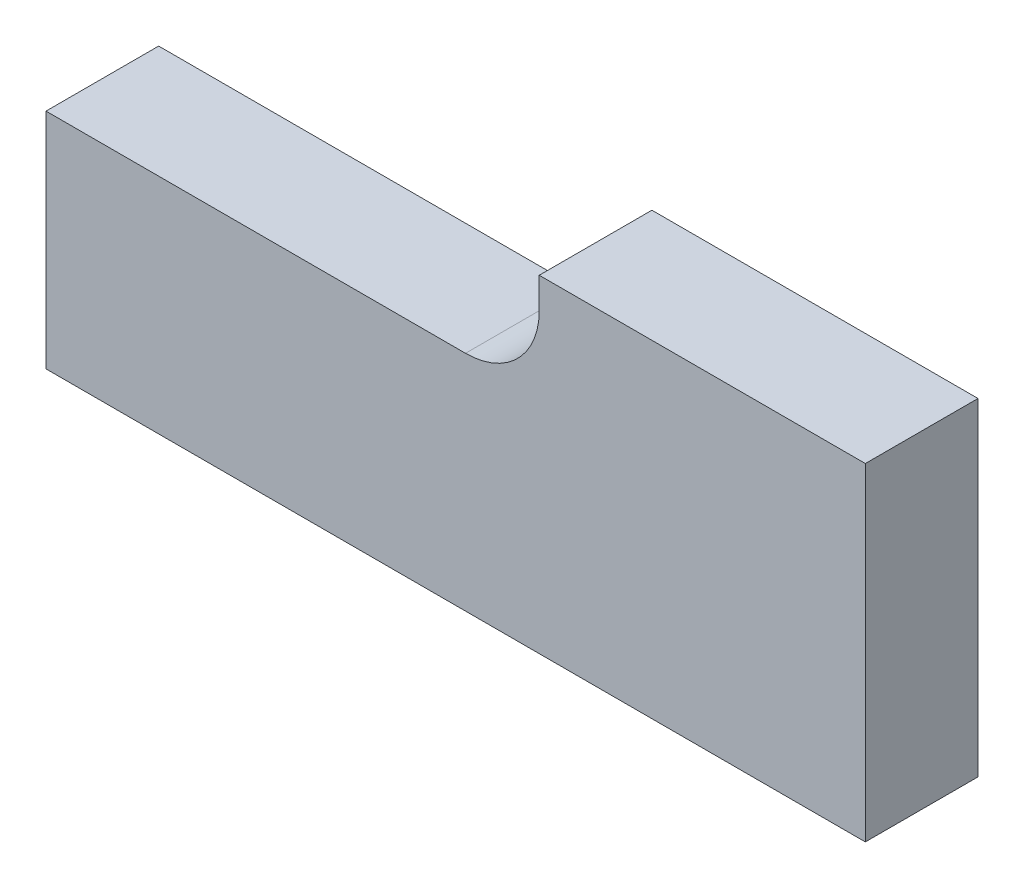
SolidWorks part; units mm, degrees
material "6063-T6"
ref_plane "Front Plane" through (0, 0, 0) normal (0, 0, 1) x (1, 0, 0)
ref_plane "Top Plane" through (0, 0, 0) normal (0, 1, 0) x (1, 0, 0)
ref_plane "Right Plane" through (0, 0, 0) normal (1, 0, 0) x (0, 0, -1)
sketch "Sketch1" plane through (0, 0, 0) normal (0, 0, 1) x (1, 0, 0)
  line L0 (0, 0) -> (0, 34.6075)
  line L1 (0, 34.6075) -> (65.024, 34.6075)
  line L2 (76.454, 46.0375) -> (76.454, 50.8)
  line L3 (76.454, 50.8) -> (127, 50.8)
  line L4 (127, 50.8) -> (127, 0)
  line L5 (127, 0) -> (0, 0)
  arc A0 (65.024, 34.6075) -> (76.454, 46.0375) centre (65.024, 46.0375) ccw
  dimension "D1" = 11.43
  dimension "D2" = 127
  dimension "D3" = 65.024
  dimension "D4" = 50.8
  dimension "D5" = 4.7625
extrude "Boss-Extrude2" add sketch "Sketch1" along normal blind 17.4625
fillet "Fillet1" [suppressed] radius 17.4625
sketch "Sketch2" [suppressed] plane through (0, 0, 0) normal (1, 0, 0) x (0, 0, -1)
  line L1 (0, 50.8) -> (-1.5875, 50.8)
  line L2 (0, 50.8) -> (0, 0)
  line L3 (0, 0) -> (-1.5875, 0)
  line L4 (-1.5875, 50.8) -> (-1.5875, 0)
  dimension "D1" = 50.8
  dimension "D2" = 1.5875
extrude "Cut-Extrude2" [suppressed] cut sketch "Sketch2" along normal through all both and the other way through all
fillet "Fillet2" [suppressed] radius 3.175
fillet "Fillet3" [suppressed] radius 1.5875
sketch "Sketch3" [suppressed] plane through (0, 0, 1.5875) normal (0, 0, -1) x (-1, 0, 0)
  line L0 (0, 1.9082) -> (0, 32.6993) construction
  line L1 (-123.0079, 50.8) -> (-80.4461, 50.8) construction
  circle A0 centre (-101.6, 39.2176) radius 6.35
  dimension "D1" = 101.6
  dimension "D3" = 12.7
  dimension "D2" = 11.5824
extrude "Cut-Extrude3" [suppressed] cut sketch "Sketch3" against normal through all
hole_wizard "1/4-20 Tapped Hole1" [suppressed] positions "Sketch4" profile "Sketch5" tap size "1/4-20" standard "ANSI Inch"
sketch "Sketch4" [suppressed] plane through (0, 0, 1.5875) normal (0, 0, -1) x (-1, 0, 0)
  line L0 (-123.0079, 50.8) -> (-80.4461, 50.8) construction
  line L1 (0, 1.9082) -> (0, 32.6993) construction
  point P0 (-12.7, 17.526)
  point P2 (-50.8, 17.526)
  dimension "D1" = 33.274
  dimension "D2" = 12.7
  dimension "D3" = 38.1
sketch "Sketch5" plane through (12.7, 17.526, 1.5875) normal (1, 0, 0) x (0, 1, 0)
  line L0 (0, 0) -> (0, 15.875)
  line L1 (0, 15.875) -> (2.5527, 15.875)
  line L2 (2.5527, 15.875) -> (2.5527, 0)
  line L5 (2.5527, 0) -> (0, 0)
  line L11 (0, -6.35) -> (0, 107.95) construction
  dimension "Thru Tap Drill Dia." = 5.1054
  dimension "Thru Tap Drill Depth" = 15.875
cosmetic thread "Hole Thread1" [suppressed] parameters "D2"=6.35
cosmetic thread "Hole Thread2" [suppressed] parameters "D2"=6.35
